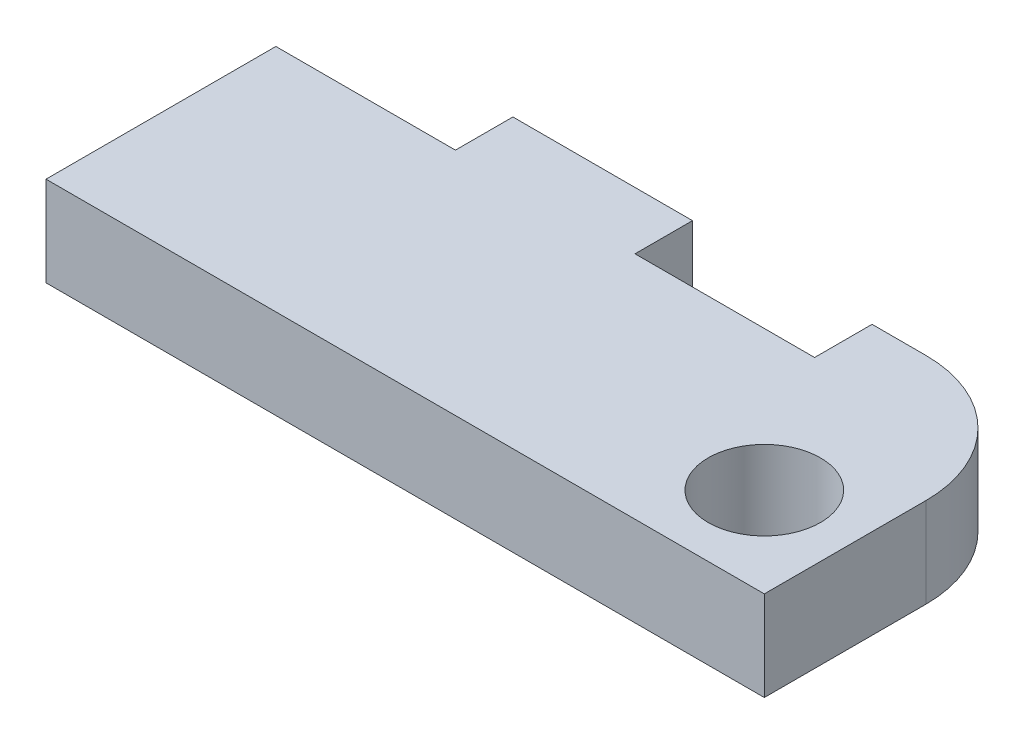
SolidWorks part; units mm, degrees
ref_plane "Plan de face" through (0, 0, 0) normal (0, 0, 1) x (1, 0, 0)
ref_plane "Plan de dessus" through (0, 0, 0) normal (0, 1, 0) x (1, 0, 0)
ref_plane "Plan de droite" through (0, 0, 0) normal (1, 0, 0) x (0, 0, -1)
sketch "Esquisse1" plane through (0, 0, 0) normal (0, 0, 1) x (1, 0, 0)
  line L1 (0, 0) -> (40, 0)
  line L2 (0, 0) -> (0, -5)
  line L3 (0, -5) -> (40, -5)
  line L4 (40, 0) -> (40, -5)
  dimension "D1" = 40
  dimension "D2" = 5
extrude "Boss.-Extru.1" add sketch "Esquisse1" along normal blind 10
sketch "Esquisse2" plane through (0, 0, 0) normal (0, 1, 0) x (1, 0, 0)
  line L1 (40, -10) -> (40, 0) construction
  circle A0 centre (35, -5) radius 3.125
  point P4 (40, -5)
  dimension "D1" = 6.25
  dimension "D2" = 5
extrude "Enlèv. mat.-Extru.1" cut sketch "Esquisse2" against normal through all
sketch "Esquisse3" plane through (0, 0, 0) normal (0, 0, -1) x (-1, 0, 0)
  line L0 (-40, -5) -> (-40, 0) construction
  line L1 (0, -5) -> (-40, -5)
  line L2 (0, -5) -> (0, 0)
  line L3 (0, 0) -> (-40, 0)
  line L4 (-40, -5) -> (-40, 0)
extrude "Boss.-Extru.2" add sketch "Esquisse3" along normal blind 6
fillet "Congé1" radius 7 1 edges at (40, -2.5, -6)
sketch "Esquisse5" plane through (0, 0, -6) normal (0, 0, -1) x (-1, 0, 0)
  line L0 (0, 0) -> (-33, 0) construction
  line L1 (0, -5) -> (-10, -5)
  line L2 (0, -5) -> (0, 0)
  line L3 (0, 0) -> (-10, 0)
  line L4 (-10, -5) -> (-10, 0)
  dimension "D1" = 10
extrude "Enlèv. mat.-Extru.3" cut sketch "Esquisse5" against normal blind 3.2
pattern_linear "Répétition linéaire1" count 2 spacing 20 along (1, 0, 0) of "Enlèv. mat.-Extru.3"
